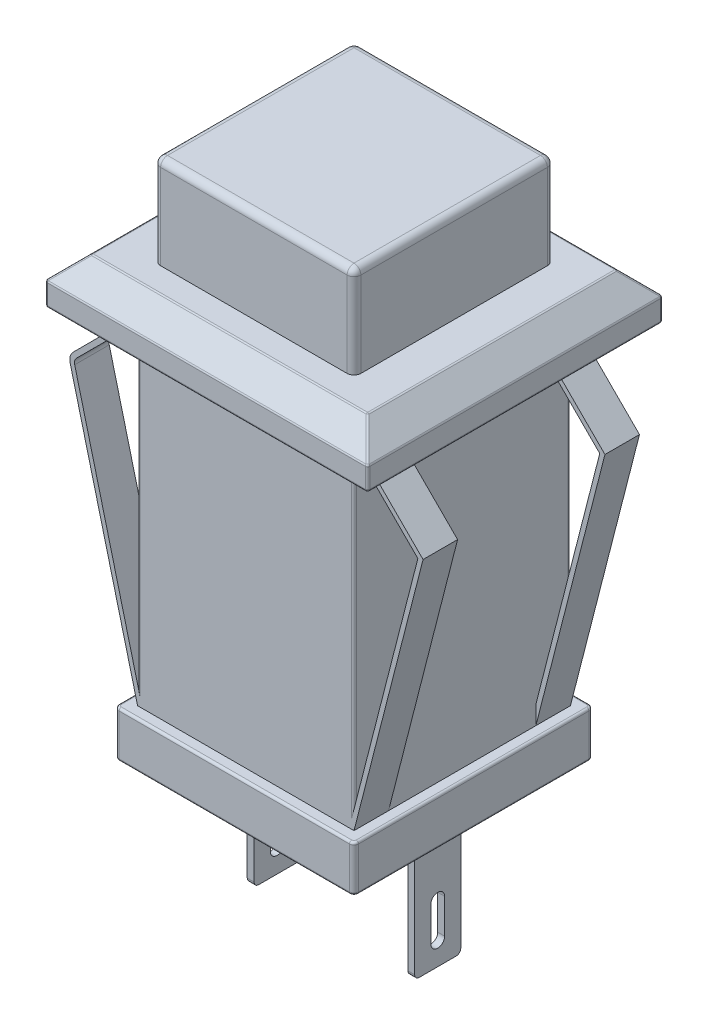
SolidWorks part; units mm, degrees
ref_plane "Front" through (0, 0, 0) normal (0, 0, 1) x (1, 0, 0)
ref_plane "Top" through (0, 0, 0) normal (0, 1, 0) x (1, 0, 0)
ref_plane "Right" through (0, 0, 0) normal (1, 0, 0) x (0, 0, -1)
sketch "Sketch1" plane through (0, 0, 0) normal (0, 1, 0) x (1, 0, 0)
  line L1 (-4.05, 4.35) -> (4.05, 4.35)
  line L2 (-4.35, 4.05) -> (-4.35, -4.05)
  line L3 (-4.05, -4.35) -> (4.05, -4.35)
  line L4 (4.35, 4.05) -> (4.35, -4.05)
  line L5 (-4.35, 4.35) -> (4.35, -4.35) construction
  line L6 (-4.35, -4.35) -> (4.35, 4.35) construction
  arc A0 (-4.35, -4.05) -> (-4.05, -4.35) centre (-4.05, -4.05) ccw
  arc A1 (4.35, -4.05) -> (4.05, -4.35) centre (4.05, -4.05) cw
  arc A2 (4.35, 4.05) -> (4.05, 4.35) centre (4.05, 4.05) ccw
  arc A3 (-4.05, 4.35) -> (-4.35, 4.05) centre (-4.05, 4.05) ccw
  point P0 (0, 0)
  dimension "D3" = 0.3
  dimension "D1" = 8.7
  dimension "D2" = 8.7
extrude "Boss-Extrude1" add sketch "Sketch1" along normal blind 4
sketch "Sketch2" plane through (0, 0, 0) normal (0, -1, 0) x (1, 0, 0)
  line L1 (-7, 6.4089) -> (7, 6.4089)
  line L2 (-7, 6.4089) -> (-7, -6.4089)
  line L3 (-7, -6.4089) -> (7, -6.4089)
  line L4 (7, 6.4089) -> (7, -6.4089)
  line L5 (-7, 6.4089) -> (7, -6.4089) construction
  line L6 (-7, -6.4089) -> (7, 6.4089) construction
  point P0 (0, 0)
  dimension "D1" = 14
  dimension "D2" = 12.8178
extrude "Boss-Extrude3" add sketch "Sketch2" along normal blind 2 separate body
chamfer "Chamfer1" distance 1 angle 45 4 edges at (7, 0, 0) (0, 0, 6.4089) (0, 0, -6.4089) (-7, 0, 0)
fillet "Fillet1" radius 0.3 8 edges at (-4.35, 4, 0) (-4.2621, 4, -4.2621) (0, 4, -4.35) (4.2621, 4, -4.2621) (4.35, 4, 0) (4.2621, 4, 4.2621) (0, 4, 4.35) (-4.2621, 4, 4.2621)
sketch "Sketch3" plane through (0, -2, 0) normal (0, -1, 0) x (1, 0, 0)
  line L1 (-5.2, 5.2) -> (5.2, 5.2)
  line L2 (-5.2, 5.2) -> (-5.2, -5.2)
  line L3 (-5.2, -5.2) -> (5.2, -5.2)
  line L4 (5.2, 5.2) -> (5.2, -5.2)
  line L5 (-5.2, 5.2) -> (5.2, -5.2) construction
  line L6 (-5.2, -5.2) -> (5.2, 5.2) construction
  point P0 (0, 0)
  dimension "D1" = 10.4
  dimension "D2" = 10.4
extrude "Boss-Extrude4" add sketch "Sketch3" along normal blind 16.7 separate body
sketch "Sketch4" plane through (0, -18.7, 0) normal (0, -1, 0) x (1, 0, 0)
  line L0 (4.7, -4.7) -> (4.7, 4.7)
  line L1 (4.7, 4.7) -> (-4.7, 4.7)
  line L2 (-4.7, 4.7) -> (-4.7, -4.7)
  line L3 (-4.7, -4.7) -> (4.7, -4.7)
  line L4 (5.2, -5.2) -> (5.2, 5.2)
  line L5 (5.2, 5.2) -> (-5.2, 5.2)
  line L6 (-5.2, 5.2) -> (-5.2, -5.2)
  line L7 (-5.2, -5.2) -> (5.2, -5.2)
  line L8 (5.2, -5.2) -> (5.2, 5.2) construction
  line L9 (5.2, 5.2) -> (-5.2, 5.2) construction
  line L10 (-5.2, 5.2) -> (-5.2, -5.2) construction
  line L11 (-5.2, -5.2) -> (5.2, -5.2) construction
  line M5 (5.2, -5.2) -> (5.2, 5.2)
  line M6 (5.2, 5.2) -> (-5.2, 5.2)
  line M7 (-5.2, 5.2) -> (-5.2, -5.2)
  line M8 (-5.2, -5.2) -> (5.2, -5.2)
  dimension "D1" = 0
  dimension "D2" = 0.5
extrude "Cut-Extrude2" cut sketch "Sketch4" against normal up to surface (14.7 mm away) from offset 2 contours L3 L2 L1 L0 M8 M5 M6 M7 up to face at (0, -2, 0) offset against normal yes
sketch "Sketch6" plane through (0, 0, -4.7) normal (0, 0, -1) x (-1, 0, 0)
  line L0 (4.7, -16.7) -> (7.7, -5)
  line L1 (7.7, -5) -> (4.7, -2)
  line L2 (4.7, -2) -> (4.7, -2.3)
  line L3 (4.7, -2) -> (4.7, -16.7) construction
  line L4 (4.7, -2.3) -> (7.4744, -5.0744)
  line L5 (7.4744, -5.0744) -> (4.7, -15.8948)
  line L6 (4.7, -15.8948) -> (4.7, -16.7)
  line L7 (7, -2) -> (-7, -2) construction
  line L8 (0, -2) -> (0, -16.7) construction
  line L9 (-4.7, -2) -> (4.7, -2) construction
  line L10 (5.2, -16.7) -> (-5.2, -16.7) construction
  line L11 (-4.7, -15.8948) -> (-4.7, -16.7)
  line L12 (-7.4744, -5.0744) -> (-4.7, -15.8948)
  line L13 (-4.7, -2.3) -> (-7.4744, -5.0744)
  line L14 (-4.7, -2) -> (-4.7, -2.3)
  line L15 (-7.7, -5) -> (-4.7, -2)
  line L16 (-4.7, -16.7) -> (-7.7, -5)
  dimension "D1" = 0.3
  dimension "D2" = 3
  dimension "D3" = 3
  dimension "D4" = 0.2
extrude "Boss-Extrude5" add sketch "Sketch6" against normal blind 1.5 separate body
fillet "Fillet2" radius 0.3 1 edges at (-7.4744, -5.0744, -3.95)
fillet "Fillet3" radius 0.5 1 edges at (-7.7, -5, -3.95)
mirror "Mirror3" about plane through (0, 0, 0) normal (0, 0, 1) of "Fillet3", "Fillet2", "Boss-Extrude5"
sketch "Sketch7" plane through (0, -18.7, 0) normal (0, -1, 0) x (1, 0, 0)
  line L0 (-3.3371, 0) -> (0, 0) construction
  line L1 (-3.6371, 1) -> (-3.3371, 1)
  line L2 (-3.6371, 1) -> (-3.6371, -1)
  line L3 (-3.6371, -1) -> (-3.3371, -1)
  line L4 (-3.3371, 1) -> (-3.3371, -1)
  line L5 (0, 0) -> (0, 5.2) construction
  line L6 (5.2, 5.2) -> (-5.2, 5.2) construction
  line L7 (3.3371, 1) -> (3.3371, -1)
  line L8 (3.6371, -1) -> (3.3371, -1)
  line L9 (3.6371, 1) -> (3.6371, -1)
  line L10 (3.6371, 1) -> (3.3371, 1)
  dimension "D1" = 0.3
  dimension "D2" = 2
extrude "Boss-Extrude6" add sketch "Sketch7" along normal blind 6
sketch "Sketch8" plane through (-3.6371, 0, 0) normal (-1, 0, 0) x (0, 0, 1)
  line L0 (0, -22.2) -> (0, -23.7) construction
  line L1 (0.3, -22.2) -> (0.3, -23.7)
  line L2 (-0.3, -22.2) -> (-0.3, -23.7)
  line L3 (1, -24.7) -> (-1, -24.7) construction
  arc A0 (0.3, -22.2) -> (-0.3, -22.2) centre (0, -22.2) ccw
  arc A1 (-0.3, -23.7) -> (0.3, -23.7) centre (0, -23.7) ccw
  point P3 (0, -22.95)
  dimension "D3" = 0.3
  dimension "D1" = 1
  dimension "D2" = 1.5
extrude "Cut-Extrude3" cut sketch "Sketch8" against normal up to surface (7.9871 mm away)
fillet "Fillet4" radius 0.2 8 edges at (-5.2, -17.7, -5.2) (5.2, -17.7, -5.2) (5.2, -17.7, 5.2) (-5.2, -17.7, 5.2) (-3.4871, -24.7, -1) (-3.4871, -24.7, 1) (3.4871, -24.7, 1) (3.4871, -24.7, -1)
sketch "Sketch9" plane through (0, -18.7, 0) normal (0, -1, 0) x (1, 0, 0)
  circle A0 centre (0, 0) radius 0.5
  dimension "D1" = 1
extrude "Cut-Extrude4" cut sketch "Sketch9" against normal blind 10
fillet "Fillet5" radius 0.1 20 edges at (5.2, -18.7, 0) (5.1414, -18.7, -5.1414) (0, -18.7, -5.2) (-5.1414, -18.7, -5.1414) (-5.2, -18.7, 0) (-5.1414, -18.7, 5.1414) (0, -18.7, 5.2) (0, -16.7, 5.2) (-5.1414, -16.7, 5.1414) (-5.2, -16.7, 0) (-5.1414, -16.7, -5.1414) (0, -16.7, -5.2) (5.1414, -16.7, -5.1414) (5.2, -16.7, 0) (5.1414, -18.7, 5.1414) (5.1414, -16.7, 5.1414) (4.7, -9.35, -4.7) (-4.7, -9.35, -4.7) (4.7, -9.0974, 4.7) (-4.7, -9.0974, 4.7)
fillet "Fillet6" radius 0.1 20 edges at (-7, -1.5, -6.4089) (7, -1.5, -6.4089) (-7, -1.5, 6.4089) (7, -1.5, 6.4089) (6.5, -0.5, -5.9089) (6, 0, 0) (6.5, -0.5, 5.9089) (7, -1, 0) (7, -2, 0) (0, -2, 6.4089) (0, -1, 6.4089) (0, 0, 5.4089) (-6.5, -0.5, 5.9089) (-7, -2, 0) (0, -2, -6.4089) (0, 0, -5.4089) (0, -1, -6.4089) (-6, 0, 0) (-7, -1, 0) (-6.5, -0.5, -5.9089)
